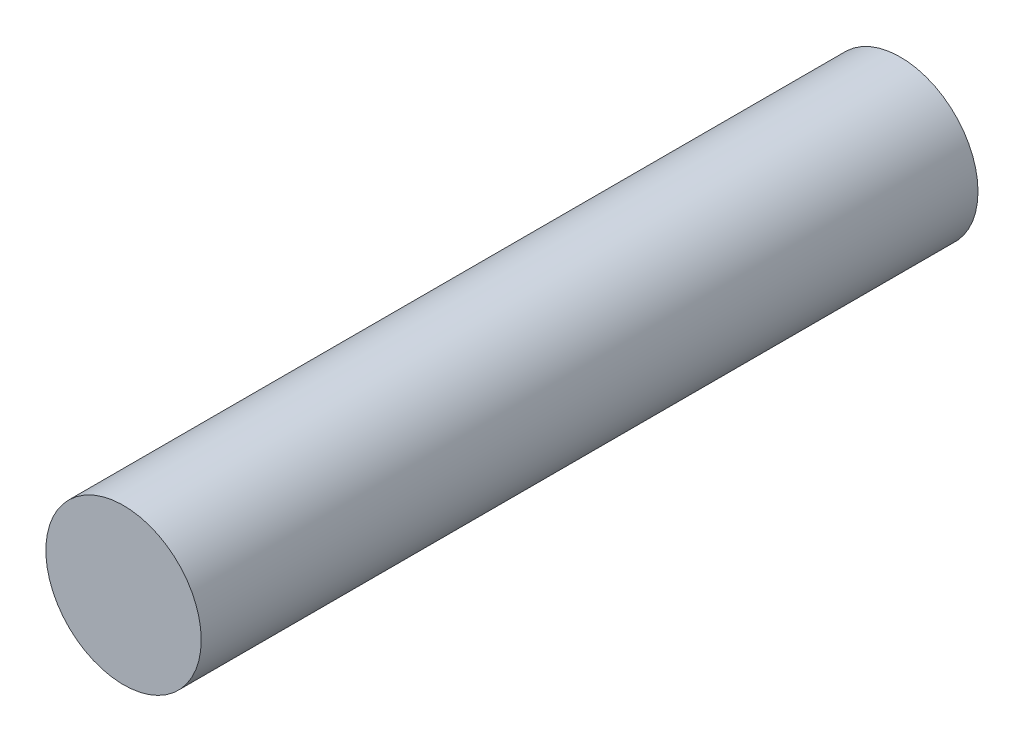
SolidWorks part; units mm, degrees
ref_plane "Front Plane" through (0, 0, 0) normal (0, 0, 1) x (1, 0, 0)
ref_plane "Top Plane" through (0, 0, 0) normal (0, 1, 0) x (1, 0, 0)
ref_plane "Right Plane" through (0, 0, 0) normal (1, 0, 0) x (0, 0, -1)
sketch "Sketch2" plane through (0, 0, 0) normal (0, 0, 1) x (1, 0, 0)
  circle A0 centre (0, 0) radius 10
extrude "Boss-Extrude1" add sketch "Sketch2" along normal blind 100
